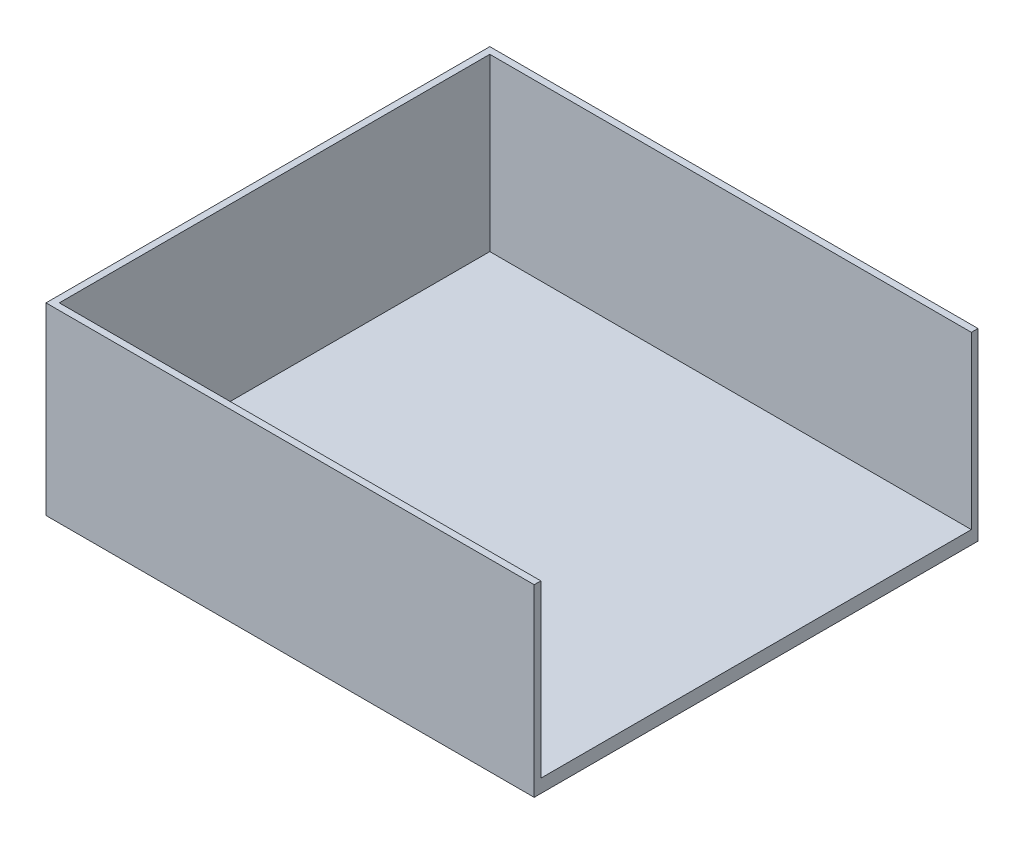
SolidWorks part; units mm, degrees
ref_plane "Front Plane" through (0, 0, 0) normal (0, 0, 1) x (1, 0, 0)
ref_plane "Top Plane" through (0, 0, 0) normal (0, 1, 0) x (1, 0, 0)
ref_plane "Right Plane" through (0, 0, 0) normal (1, 0, 0) x (0, 0, -1)
sketch "Sketch1" plane through (0, 0, 0) normal (0, 1, 0) x (1, 0, 0)
  line L1 (-107.5062, -112.5425) -> (112.4938, -112.5425)
  line L2 (-107.5062, -112.5425) -> (-107.5062, 87.4575)
  line L3 (-107.5062, 87.4575) -> (112.4938, 87.4575)
  line L4 (112.4938, -112.5425) -> (112.4938, 87.4575)
  dimension "D1" = 220
  dimension "D2" = 200
extrude "Boss-Extrude1" add sketch "Sketch1" along normal blind 3 contours L1 L4 L3 L2
sketch "Sketch3" plane through (0, 3, 0) normal (0, 1, 0) x (1, 0, 0)
  line L0 (112.4938, -112.5425) -> (-107.5062, -112.5425)
  line L1 (-107.5062, -112.5425) -> (-107.5062, 87.4575)
  line L2 (-107.5062, 87.4575) -> (112.4938, 87.4575)
  line L7 (-107.5062, 87.4575) -> (-107.5062, -112.5425)
  line L8 (-107.5062, -112.5425) -> (112.4938, -112.5425)
  line L9 (112.4938, -112.5425) -> (112.4938, 87.4575)
  line L10 (112.4938, 87.4575) -> (-107.5062, 87.4575)
  line L13 (112.4938, -112.5425) -> (112.4938, 87.4575)
  dimension "D1" = 0
extrude "Boss-Extrude3" add sketch "Sketch3" along normal blind 80 contours L2 L13 L0 L1
sketch "Sketch9" plane through (0, 83, 0) normal (0, 1, 0) x (1, 0, 0)
  line L8 (-104.5062, 84.4575) -> (-104.5062, -109.5425)
  line L9 (-104.5062, -109.5425) -> (109.4938, -109.5425)
  line L10 (109.4938, -109.5425) -> (109.4938, 84.4575)
  line L11 (109.4938, 84.4575) -> (-104.5062, 84.4575)
  line L12 (-104.5062, 84.4575) -> (-104.5062, -109.5425)
  line L13 (-104.5062, -109.5425) -> (109.4938, -109.5425)
  line L14 (109.4938, -109.5425) -> (109.4938, 84.4575)
  line L15 (109.4938, 84.4575) -> (-104.5062, 84.4575)
  dimension "D1" = 3
extrude "Cut-Extrude1" cut sketch "Sketch9" against normal blind 77
sketch "Sketch13" plane through (109.4938, 0, 0) normal (-1, 0, 0) x (0, 0, 1)
  line L0 (109.5425, 6) -> (-84.4575, 6) construction
  line L1 (-84.4575, 83) -> (109.5425, 83)
  line L2 (-84.4575, 83) -> (-84.4575, 6)
  line L3 (-84.4575, 6) -> (109.5425, 6)
  line L4 (109.5425, 83) -> (109.5425, 6)
extrude "Cut-Extrude4" cut sketch "Sketch13" against normal blind 197
